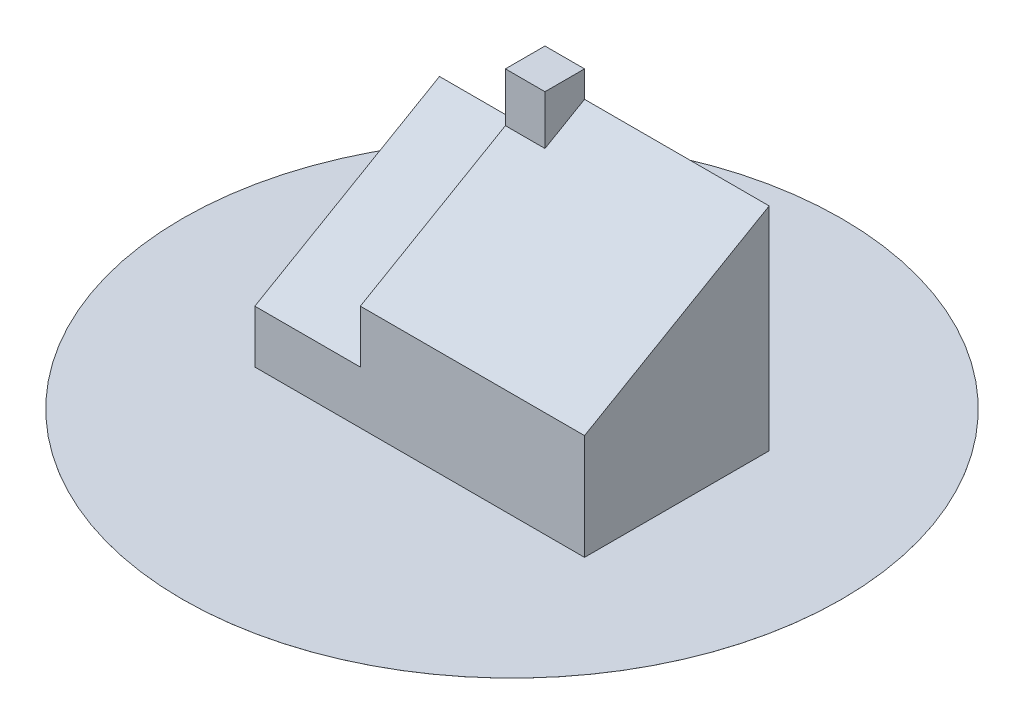
SolidWorks part; units mm, degrees
ref_plane "Front" through (0, 0, 0) normal (0, 0, 1) x (1, 0, 0)
ref_plane "Top" through (0, 0, 0) normal (0, 1, 0) x (1, 0, 0)
ref_plane "Right" through (0, 0, 0) normal (1, 0, 0) x (0, 0, -1)
sketch "Sketch1" plane through (0, 0, 0) normal (0, 1, 0) x (1, 0, 0)
  line L1 (0, 0) -> (125, 0)
  line L2 (0, 0) -> (0, -70)
  line L3 (0, -70) -> (125, -70)
  line L4 (125, 0) -> (125, -70)
  dimension "D1" = 70
  dimension "D2" = 125
extrude "Extrude1" add sketch "Sketch1" along normal blind 20
sketch "Sketch2" plane through (0, 0, 0) normal (-1, 0, 0) x (0, 0, 1)
  line L0 (0, 20) -> (70, 20)
  line L1 (70, 20) -> (0, 60.4145)
  line L2 (0, 60.4145) -> (0, 20)
  dimension "D1" = 30
extrude "Extrude2" add sketch "Sketch2" against normal blind 40
sketch "Sketch3" plane through (125, 0, 0) normal (1, 0, 0) x (0, 0, -1)
  line L0 (-70, 20) -> (-70, 40)
  line L1 (-70, 40) -> (0, 80.4145)
  line L2 (0, 80.4145) -> (0, 20)
  line L3 (-70, 20) -> (0, 20) construction
  line L4 (0, 20) -> (-70, 20)
  dimension "D1" = 20
  dimension "D2" = 30
extrude "Extrude3" add sketch "Sketch3" against normal blind 85
ref_plane "Plane1" through (0, 80.4145, 0) normal (0, 1, 0) x (-1, 0, 0)
sketch "Sketch5" plane through (0, 80.4145, 0) normal (0, 1, 0) x (-1, 0, 0)
  line L1 (-40, 0) -> (-55, 0)
  line L2 (-40, 0) -> (-40, 15)
  line L3 (-40, 15) -> (-55, 15)
  line L4 (-55, 0) -> (-55, 15)
  dimension "D1" = 15
  dimension "D2" = 15
extrude "Extrude5" add sketch "Sketch5" along normal blind 10 and the other way blind 20
sketch "Sketch6" plane through (0, 0, 0) normal (0, 1, 0) x (1, 0, 0)
  line L0 (125, 0) -> (0, -70) construction
  circle A0 centre (62.5, -35) radius 125
  dimension "D1" = 250
extrude "Extrude6" add sketch "Sketch6" along normal blind 0.01
